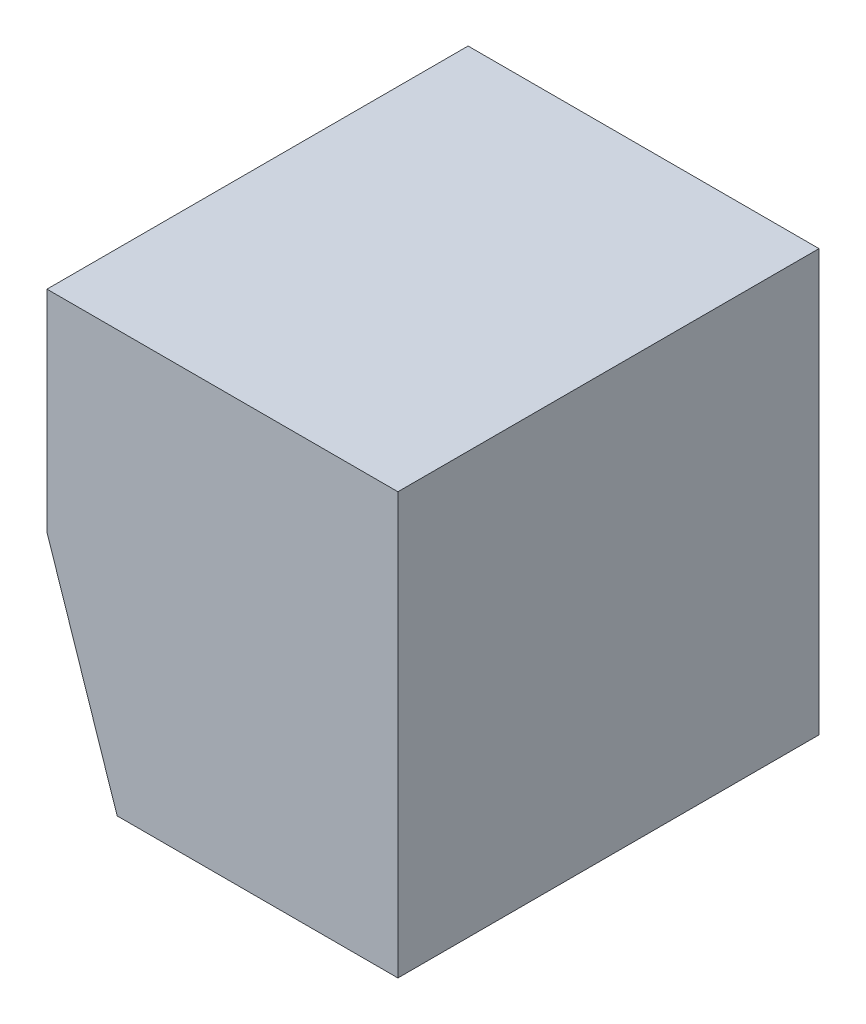
SolidWorks part; units mm, degrees
ref_plane "Спереди" through (0, 0, 0) normal (0, 0, 1) x (1, 0, 0)
ref_plane "Сверху" through (0, 0, 0) normal (0, 1, 0) x (1, 0, 0)
ref_plane "Справа" through (0, 0, 0) normal (1, 0, 0) x (0, 0, -1)
sketch "Эскиз1" plane through (0, 0, 0) normal (0, 0, 1) x (1, 0, 0)
  line L0 (0, 0) -> (0, -15)
  line L1 (0, -15) -> (5, -30)
  line L2 (5, -30) -> (25, -30)
  line L3 (25, -30) -> (25, 0)
  line L4 (25, 0) -> (0, 0)
  dimension "D1" = 30
  dimension "D2" = 25
  dimension "D3" = 15
  dimension "D4" = 20
extrude "Бобышка-Вытянуть1" add sketch "Эскиз1" along normal blind 30
sketch "Эскиз2" plane through (-4.5, -1.5, 0) normal (-0.9487, -0.3162, 0) x (0, 0, 1)
  line L0 (0, -30.0416) -> (30, -14.2302) construction
  line L1 (0, -14.2302) -> (30, -30.0416) construction
  point P8 (15, -22.1359)
